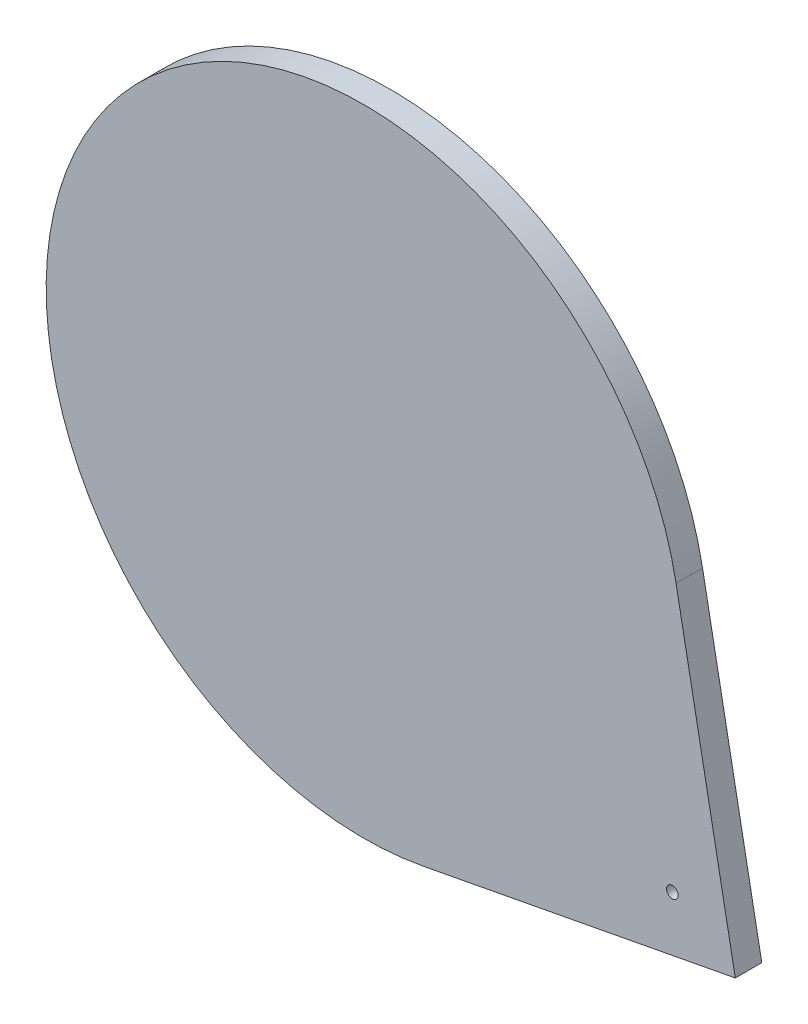
SolidWorks part; units mm, degrees
ref_plane "Front Plane" through (0, 0, 0) normal (0, 0, 1) x (1, 0, 0)
ref_plane "Top Plane" through (0, 0, 0) normal (0, 1, 0) x (1, 0, 0)
ref_plane "Right Plane" through (0, 0, 0) normal (1, 0, 0) x (0, 0, -1)
sketch "Sketch1" plane through (0, 0, 0) normal (0, 0, 1) x (1, 0, 0)
  line L0 (58.9481, 11.186) -> (70.1341, -47.762)
  line L1 (70.1341, -47.762) -> (11.186, -58.9481)
  line L2 (70.1341, -47.762) -> (49.5923, -33.7728) construction
  line L3 (58.2459, -39.666) -> (68.238, -37.7699) construction
  line L4 (58.2459, -39.666) -> (60.142, -49.6581) construction
  arc A0 (58.9481, 11.186) -> (11.186, -58.9481) centre (0, 0) ccw
  circle A1 centre (58.2459, -39.666) radius 1.1
  point P9 (46.3577, -31.5701)
  point P11 (0, 0)
  point P12 (0, 0)
  point P13 (35.2944, -24.0359)
  dimension "D1" = 120
  dimension "D2" = 2.2
  dimension "D3" = 11.186
  dimension "D4" = 58.2459
extrude "Boss-Extrude1" add sketch "Sketch1" along normal blind 5
